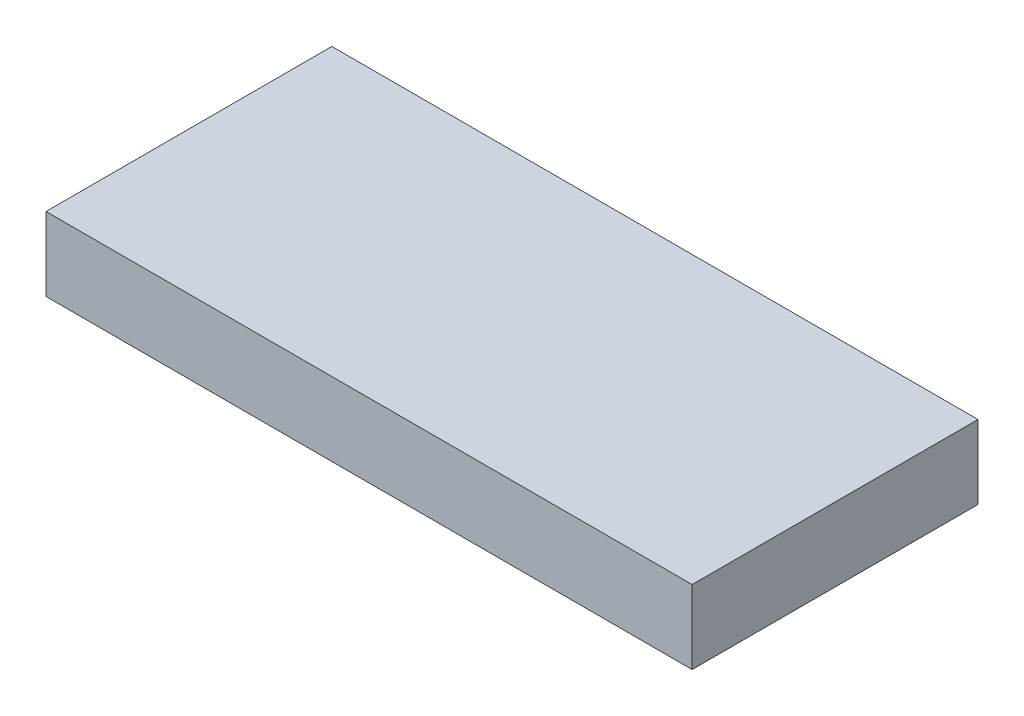
SolidWorks part; units mm, degrees
ref_plane "Front Plane" through (0, 0, 0) normal (0, 0, 1) x (1, 0, 0)
ref_plane "Top Plane" through (0, 0, 0) normal (0, 1, 0) x (1, 0, 0)
ref_plane "Right Plane" through (0, 0, 0) normal (1, 0, 0) x (0, 0, -1)
sketch "Sketch1" plane through (0, 0, 0) normal (0, 1, 0) x (1, 0, 0)
  line L0 (-82.5, -36.5) -> (82.5, -36.5)
  line L1 (-82.5, -36.5) -> (-82.5, 36.5)
  line L2 (82.5, -36.5) -> (82.5, 36.5)
  line L3 (-82.5, 36.5) -> (82.5, 36.5)
  line L4 (-82.5, -36.5) -> (82.5, 36.5) construction
  line L5 (82.5, -36.5) -> (-82.5, 36.5) construction
  point P1 (0, 0)
  dimension "D1" = 165
  dimension "D2" = 73
extrude "Boss-Extrude1" add sketch "Sketch1" along normal blind 18.8
